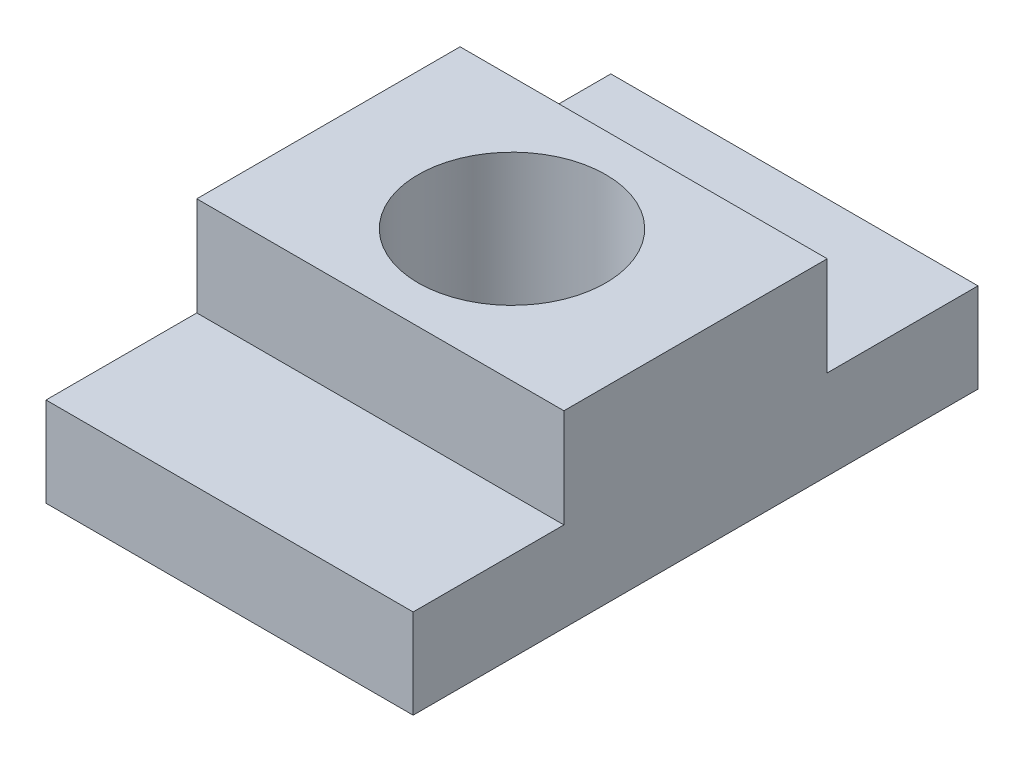
SolidWorks part; units mm, degrees
ref_plane "Front Plane" through (0, 0, 0) normal (0, 0, 1) x (1, 0, 0)
ref_plane "Top Plane" through (0, 0, 0) normal (0, 1, 0) x (1, 0, 0)
ref_plane "Right Plane" through (0, 0, 0) normal (1, 0, 0) x (0, 0, -1)
sketch "Sketch1" plane through (0, 0, 0) normal (0, 1, 0) x (1, 0, 0)
  line L1 (15.4781, 23.8125) -> (-15.4781, 23.8125)
  line L2 (15.4781, 23.8125) -> (15.4781, -23.8125)
  line L3 (15.4781, -23.8125) -> (-15.4781, -23.8125)
  line L4 (-15.4781, 23.8125) -> (-15.4781, -23.8125)
  line L5 (15.4781, 23.8125) -> (-15.4781, -23.8125) construction
  line L6 (15.4781, -23.8125) -> (-15.4781, 23.8125) construction
  circle A0 centre (0, 0) radius 7.9121
  point P0 (0, 0)
  dimension "D3" = 15.8242
  dimension "D1" = 47.625
  dimension "D2" = 30.9562
extrude "Boss-Extrude1" add sketch "Sketch1" along normal blind 7.5406
sketch "Sketch2" plane through (0, 7.5406, 0) normal (0, 1, 0) x (1, 0, 0)
  line L0 (-15.4781, 23.8125) -> (-15.4781, -23.8125) construction
  line L1 (15.4781, -11.0998) -> (-15.4781, -11.0998)
  line L2 (15.4781, -11.0998) -> (15.4781, 11.0998)
  line L3 (15.4781, 11.0998) -> (-15.4781, 11.0998)
  line L4 (-15.4781, -11.0998) -> (-15.4781, 11.0998)
  line L5 (15.4781, -11.0998) -> (-15.4781, 11.0998) construction
  line L6 (15.4781, 11.0998) -> (-15.4781, -11.0998) construction
  circle A0 centre (0, 0) radius 7.9121 construction
  circle A1 centre (0, 0) radius 7.9121
  point P0 (0, 0)
  dimension "D1" = 22.1996
extrude "Boss-Extrude2" add sketch "Sketch2" along normal blind 8.3344
